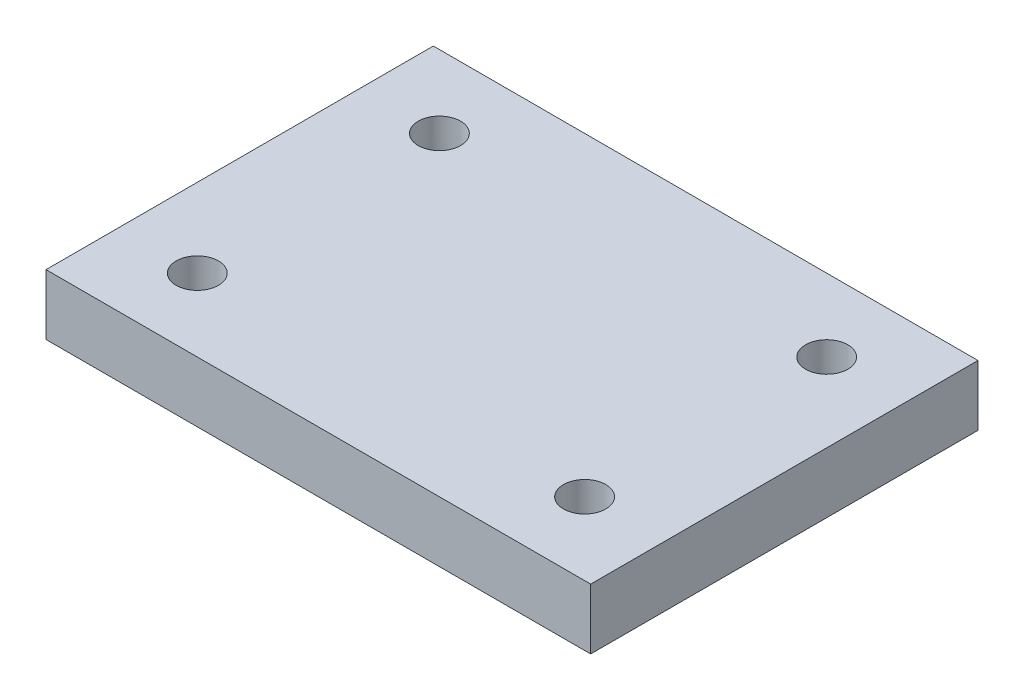
SolidWorks part; units mm, degrees
ref_plane "Front Plane" through (0, 0, 0) normal (0, 0, 1) x (1, 0, 0)
ref_plane "Top Plane" through (0, 0, 0) normal (0, 1, 0) x (1, 0, 0)
ref_plane "Right Plane" through (0, 0, 0) normal (1, 0, 0) x (0, 0, -1)
sketch "Sketch1" plane through (0, 0, 0) normal (0, 1, 0) x (1, 0, 0)
  line L1 (0, 0) -> (55, 0)
  line L2 (0, 0) -> (0, 32)
  line L3 (0, 32) -> (55, 32)
  line L4 (55, 0) -> (55, 32)
  dimension "D1" = 32
  dimension "D2" = 55
extrude "Boss-Extrude1" add sketch "Sketch1" along normal blind 50
sketch "Sketch2" plane through (0, 0, 0) normal (0, -1, 0) x (1, 0, 0)
  line L0 (0, 0) -> (55, 0) construction
  line L1 (5, 0) -> (50, 0)
  line L2 (5, 0) -> (5, -32)
  line L3 (5, -32) -> (50, -32)
  line L4 (50, 0) -> (50, -32)
  line L5 (55, -32) -> (0, -32) construction
  line L6 (0, -32) -> (0, 0) construction
  line L7 (55, 0) -> (55, -32) construction
  dimension "D1" = 5
  dimension "D2" = 5
extrude "Cut-Extrude1" cut sketch "Sketch2" against normal blind 45
sketch "Sketch3" plane through (0, 50, 0) normal (0, 1, 0) x (1, 0, 0)
  line L0 (55, 32) -> (0, 32) construction
  line L1 (55, 0) -> (55, 32) construction
  circle A0 centre (43.5, 26) radius 1.75
  circle A1 centre (43.5, 6) radius 1.75
  circle A2 centre (11.5, 26) radius 1.75
  circle A3 centre (11.5, 6) radius 1.75
  dimension "D1" = 3.5
  dimension "D2" = 20
  dimension "D3" = 20
  dimension "D4" = 32
  dimension "D5" = 32
  dimension "D6" = 6
  dimension "D7" = 11.5
extrude "Cut-Extrude2" cut sketch "Sketch3" against normal through all
sketch "Sketch4" plane through (55, 0, 0) normal (1, 0, 0) x (0, 0, -1)
  line L0 (0, 50) -> (32, 50) construction
  line L1 (0, 50) -> (0, 0) construction
  circle A0 centre (6, 5) radius 1.75
  circle A1 centre (26, 5) radius 1.75
  dimension "D1" = 3.5
  dimension "D2" = 3.5
  dimension "D3" = 20
  dimension "D4" = 45
  dimension "D5" = 6
extrude "Cut-Extrude3" cut sketch "Sketch4" against normal through all
sketch "Sketch5" plane through (50, 0, 0) normal (-1, 0, 0) x (0, 0, 1)
  line L0 (-30, 10) -> (-28.9, 10)
  line L1 (-32, 45) -> (-30.9, 45)
  line L2 (-32, 45) -> (-32, 10)
  line L3 (-32, 10) -> (-30.9, 10)
  line L4 (-30.9, 45) -> (-30.9, 10)
  line L5 (-28.9, 45) -> (-28.9, 10)
  line L6 (-30, 45) -> (-30, 10)
  line L7 (-30, 45) -> (-28.9, 45)
  line L8 (-28, 10) -> (-26.9, 10)
  line L9 (-26.9, 45) -> (-26.9, 10)
  line L10 (-28, 45) -> (-28, 10)
  line L11 (-28, 45) -> (-26.9, 45)
  line L12 (-26, 10) -> (-24.9, 10)
  line L13 (-24.9, 45) -> (-24.9, 10)
  line L14 (-26, 45) -> (-26, 10)
  line L15 (-26, 45) -> (-24.9, 45)
  line L16 (-24, 10) -> (-22.9, 10)
  line L17 (-22.9, 45) -> (-22.9, 10)
  line L18 (-24, 45) -> (-24, 10)
  line L19 (-24, 45) -> (-22.9, 45)
  line L20 (-22, 10) -> (-20.9, 10)
  line L21 (-20.9, 45) -> (-20.9, 10)
  line L22 (-22, 45) -> (-22, 10)
  line L23 (-22, 45) -> (-20.9, 45)
  line L24 (-20, 10) -> (-18.9, 10)
  line L25 (-18.9, 45) -> (-18.9, 10)
  line L26 (-20, 45) -> (-20, 10)
  line L27 (-20, 45) -> (-18.9, 45)
  line L28 (-18, 10) -> (-16.9, 10)
  line L29 (-16.9, 45) -> (-16.9, 10)
  line L30 (-18, 45) -> (-18, 10)
  line L31 (-18, 45) -> (-16.9, 45)
  line L32 (-16, 10) -> (-14.9, 10)
  line L33 (-14.9, 45) -> (-14.9, 10)
  line L34 (-16, 45) -> (-16, 10)
  line L35 (-16, 45) -> (-14.9, 45)
  line L36 (-14, 10) -> (-12.9, 10)
  line L37 (-12.9, 45) -> (-12.9, 10)
  line L38 (-14, 45) -> (-14, 10)
  line L39 (-14, 45) -> (-12.9, 45)
  line L40 (-12, 10) -> (-10.9, 10)
  line L41 (-10.9, 45) -> (-10.9, 10)
  line L42 (-12, 45) -> (-12, 10)
  line L43 (-12, 45) -> (-10.9, 45)
  line L44 (-10, 10) -> (-8.9, 10)
  line L45 (-8.9, 45) -> (-8.9, 10)
  line L46 (-10, 45) -> (-10, 10)
  line L47 (-10, 45) -> (-8.9, 45)
  line L48 (-8, 10) -> (-6.9, 10)
  line L49 (-6.9, 45) -> (-6.9, 10)
  line L50 (-8, 45) -> (-8, 10)
  line L51 (-8, 45) -> (-6.9, 45)
  line L52 (-6, 10) -> (-4.9, 10)
  line L53 (-4.9, 45) -> (-4.9, 10)
  line L54 (-6, 45) -> (-6, 10)
  line L55 (-6, 45) -> (-4.9, 45)
  line L56 (-4, 10) -> (-2.9, 10)
  line L57 (-2.9, 45) -> (-2.9, 10)
  line L58 (-4, 45) -> (-4, 10)
  line L59 (-4, 45) -> (-2.9, 45)
  line L60 (-2, 10) -> (-0.9, 10)
  line L61 (-0.9, 45) -> (-0.9, 10)
  line L62 (-2, 45) -> (-2, 10)
  line L63 (-2, 45) -> (-0.9, 45)
  line L64 (0, 10) -> (1.1, 10)
  line L65 (1.1, 45) -> (1.1, 10)
  line L66 (0, 45) -> (0, 10)
  line L67 (0, 45) -> (1.1, 45)
  dimension "D1" = 35
  dimension "D2" = 1.1
  dimension "D3" = 17
extrude "Cut-Extrude4" cut sketch "Sketch5" against normal blind 1.2
sketch "Sketch6" plane through (0, 50, 0) normal (0, 1, 0) x (1, 0, 0)
  line L0 (0, 0) -> (55, 0) construction
  line L1 (55, 32) -> (50, 32)
  line L2 (55, 32) -> (55, 0)
  line L3 (55, 0) -> (50, 0)
  line L4 (50, 32) -> (50, 0)
  line L5 (0, 32) -> (0, 0) construction
  line L6 (0, 32) -> (5, 32)
  line L7 (0, 32) -> (0, 0)
  line L8 (0, 0) -> (5, 0)
  line L9 (5, 32) -> (5, 0)
  line L10 (55, 32) -> (0, 32) construction
  dimension "D1" = 5
  dimension "D2" = 5
extrude "Cut-Extrude5" cut sketch "Sketch6" against normal through all
